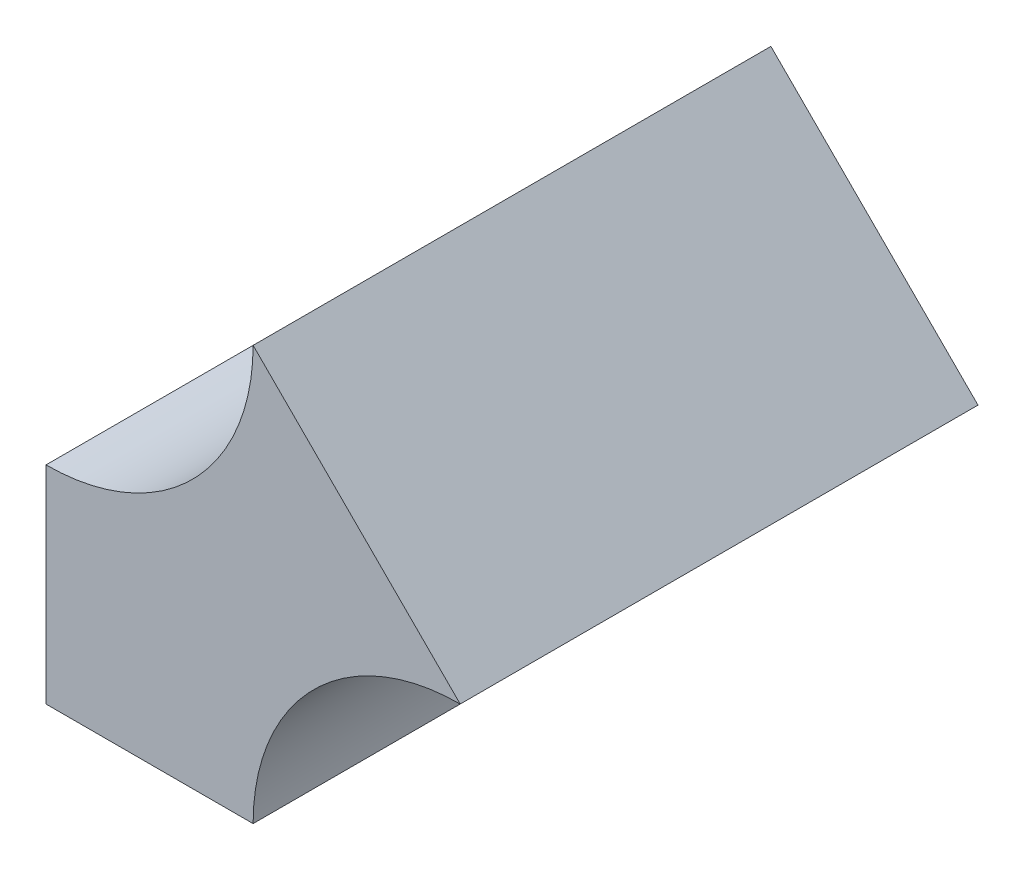
SolidWorks part; units mm, degrees
ref_plane "Front Plane" through (0, 0, 0) normal (0, 0, 1) x (1, 0, 0)
ref_plane "Top Plane" through (0, 0, 0) normal (0, 1, 0) x (1, 0, 0)
ref_plane "Right Plane" through (0, 0, 0) normal (1, 0, 0) x (0, 0, -1)
sketch "Sketch1" plane through (0, 0, 0) normal (0, 0, 1) x (1, 0, 0)
  line L0 (-10, 10) -> (-10, 0)
  line L1 (-10, 0) -> (0, 0)
  line L2 (10, 10) -> (0, 20)
  arc A0 (0, 0) -> (10, 10) centre (10, 0) cw
  arc A1 (-10, 10) -> (0, 20) centre (-10, 20) ccw
  dimension "D4" = 10
  dimension "D5" = 10
  dimension "D1" = 10
  dimension "D2" = 10
  dimension "D3" = 10
extrude "Boss-Extrude1" add sketch "Sketch1" along normal blind 25
